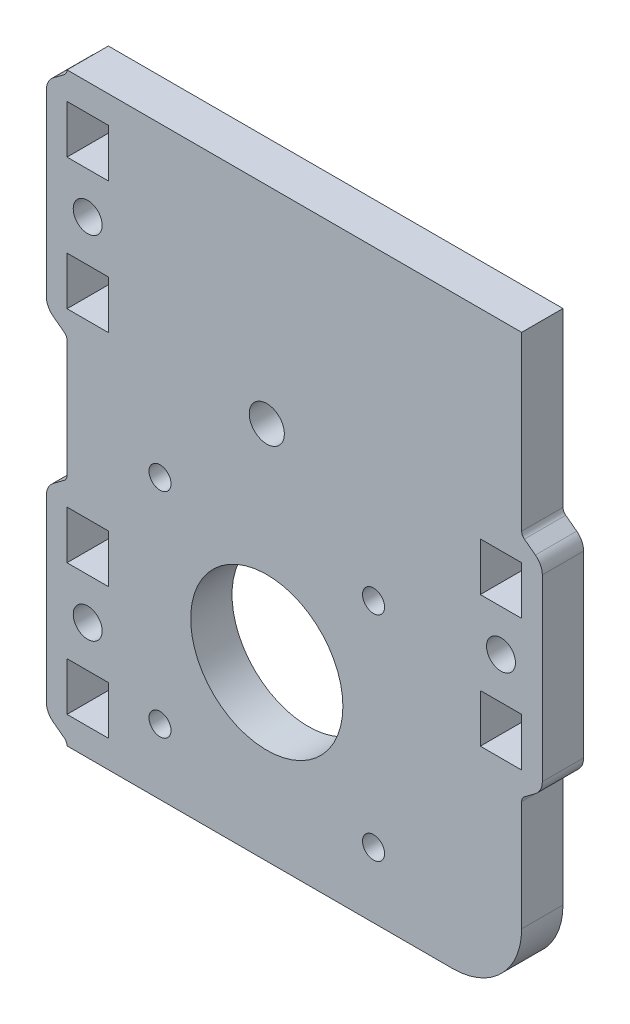
SolidWorks part; units mm, degrees
material "Клен"
ref_plane "Спереди" through (0, 0, 0) normal (0, 0, 1) x (1, 0, 0)
ref_plane "Сверху" through (0, 0, 0) normal (0, 1, 0) x (1, 0, 0)
ref_plane "Справа" through (0, 0, 0) normal (1, 0, 0) x (0, 0, -1)
sketch "Эскиз1" plane through (0, 0, 0) normal (0, 0, 1) x (1, 0, 0)
  line L7 (0, -293.8462) -> (66, -293.8462)
  line L9 (0, -378.8462) -> (0, -293.8462)
  line L11 (66, -293.8462) -> (66, -287.8462) construction
  line L12 (66, -293.8462) -> (66, -368.8462)
  line L14 (56, -378.8462) -> (0, -378.8462)
  arc A0 (66, -368.8462) -> (56, -378.8462) centre (56, -368.8462) cw
  circle A1 centre (29, -323.8462) radius 2.55
  dimension "D3" = 5.1
  dimension "D2" = 10
  dimension "D1" = 85
extrude "Бобышка-Вытянуть1" add sketch "Эскиз1" against normal blind 6 contours L14 L9 L7 L12 A0
sketch "Эскиз2" plane through (0, 0, 0) normal (0, 0, 1) x (1, 0, 0)
  line L1 (0, -378.8462) -> (0, -293.8462) construction
  line L3 (29, -353.8462) -> (54.8419, -353.8462) construction
  line L5 (0, -293.8462) -> (66, -293.8462) construction
  circle A0 centre (29, -353.8462) radius 11.05
  circle A1 centre (44.5, -369.3462) radius 1.6
  circle A2 centre (13.5, -369.3462) radius 1.6
  circle A3 centre (13.5, -338.3462) radius 1.6
  circle A4 centre (44.5, -338.3462) radius 1.6
  circle A5 centre (29, -323.8462) radius 2.55
  dimension "D2" = 22.1
  dimension "D3" = 3.2
  dimension "D6" = 5.1
  dimension "D1" = 60
  dimension "D4" = 15.5
  dimension "D5" = 15.5
  dimension "D7" = 29
extrude "Вырез-Вытянуть1" cut sketch "Эскиз2" against normal through all
sketch "Эскиз21" plane through (16, -335.8462, 0) normal (0, 0, -1) x (0, 1, 0)
  line L0 (-13, 53) -> (13, 53)
  line L2 (15, 52) -> (16.2, 50.4)
  line L4 (17, 50) -> (-17, 50)
  line L5 (-15, 52) -> (-16.2, 50.4)
  arc A6 (13, 53) -> (15, 52) centre (13, 50.5) cw
  arc A7 (16.2, 50.4) -> (17, 50) centre (17, 51) ccw
  arc A8 (-13, 53) -> (-15, 52) centre (-13, 50.5) ccw
  arc A9 (-16.2, 50.4) -> (-17, 50) centre (-17, 51) cw
  point P12 (0, 53)
  point P13 (14.118, 52.7361)
  point P15 (-14.118, 52.7361)
  point P17 (0, 50)
  point P21 (14.118, 52.7361)
  dimension "D4" = 2.5
  dimension "D5" = 1
extrude "Бобышка-Вытянуть2" add sketch "Эскиз21" along normal blind 6
sketch "Эскиз3" plane through (16, -335.8462, -6) normal (0, 0, -1) x (0, 1, 0)
  line L1 (13.0318, 50) -> (6.0318, 50)
  line L2 (13.0318, 50) -> (13.0318, 44)
  line L3 (13.0318, 44) -> (6.0318, 44)
  line L4 (6.0318, 50) -> (6.0318, 44)
  line L5 (-13.0318, 44) -> (-6.0318, 44)
  line L6 (-13.0318, 50) -> (-13.0318, 44)
  line L7 (-6.0318, 50) -> (-6.0318, 44)
  line L8 (-13.0318, 50) -> (-6.0318, 50)
  circle A0 centre (0, 47) radius 2.1
  dimension "D1" = 4.2
extrude "Вырез-Вытянуть11" cut sketch "Эскиз3" against normal through all
other "Авто-элемент1<DIN967-21>"
sketch "Эскиз22" plane through (50, -310.8462, 0) normal (0, 0, -1) x (0, -1, 0)
  line L0 (-13, 53) -> (13, 53)
  line L2 (15, 52) -> (16.2, 50.4)
  line L4 (17, 50) -> (-17, 50)
  line L5 (-15, 52) -> (-16.2, 50.4)
  arc A6 (13, 53) -> (15, 52) centre (13, 50.5) cw
  arc A7 (16.2, 50.4) -> (17, 50) centre (17, 51) ccw
  arc A8 (-13, 53) -> (-15, 52) centre (-13, 50.5) ccw
  arc A9 (-16.2, 50.4) -> (-17, 50) centre (-17, 51) cw
  point P12 (0, 53)
  point P13 (14.118, 52.7361)
  point P15 (-14.118, 52.7361)
  point P17 (0, 50)
  point P21 (14.118, 52.7361)
  dimension "D4" = 2.5
  dimension "D5" = 1
extrude "Бобышка-Вытянуть21" add sketch "Эскиз22" along normal blind 6
sketch "Эскиз31" plane through (50, -310.8462, -6) normal (0, 0, -1) x (0, -1, 0)
  line L1 (13.0318, 50) -> (6.0318, 50)
  line L2 (13.0318, 50) -> (13.0318, 44)
  line L3 (13.0318, 44) -> (6.0318, 44)
  line L4 (6.0318, 50) -> (6.0318, 44)
  line L5 (-13.0318, 44) -> (-6.0318, 44)
  line L6 (-13.0318, 50) -> (-13.0318, 44)
  line L7 (-6.0318, 50) -> (-6.0318, 44)
  line L8 (-13.0318, 50) -> (-6.0318, 50)
  circle A0 centre (0, 47) radius 2.1
  dimension "D1" = 4.2
extrude "Вырез-Вытянуть12" cut sketch "Эскиз31" against normal through all
other "Авто-элемент2<DIN967-22>"
sketch "Эскиз24" plane through (50, -361.8462, 0) normal (0, 0, -1) x (0, -1, 0)
  line L0 (-13, 53) -> (13, 53)
  line L2 (15, 52) -> (16.2, 50.4)
  line L4 (17, 50) -> (-17, 50)
  line L5 (-15, 52) -> (-16.2, 50.4)
  arc A6 (13, 53) -> (15, 52) centre (13, 50.5) cw
  arc A7 (16.2, 50.4) -> (17, 50) centre (17, 51) ccw
  arc A8 (-13, 53) -> (-15, 52) centre (-13, 50.5) ccw
  arc A9 (-16.2, 50.4) -> (-17, 50) centre (-17, 51) cw
  point P12 (0, 53)
  point P13 (14.118, 52.7361)
  point P15 (-14.118, 52.7361)
  point P17 (0, 50)
  point P21 (14.118, 52.7361)
  dimension "D4" = 2.5
  dimension "D5" = 1
extrude "Бобышка-Вытянуть24" add sketch "Эскиз24" along normal blind 6
sketch "Эскиз34" plane through (50, -361.8462, -6) normal (0, 0, -1) x (0, -1, 0)
  line L1 (13.0318, 50) -> (6.0318, 50)
  line L2 (13.0318, 50) -> (13.0318, 44)
  line L3 (13.0318, 44) -> (6.0318, 44)
  line L4 (6.0318, 50) -> (6.0318, 44)
  line L5 (-13.0318, 44) -> (-6.0318, 44)
  line L6 (-13.0318, 50) -> (-13.0318, 44)
  line L7 (-6.0318, 50) -> (-6.0318, 44)
  line L8 (-13.0318, 50) -> (-6.0318, 50)
  circle A0 centre (0, 47) radius 2.1
  dimension "D1" = 4.2
extrude "Вырез-Вытянуть15" cut sketch "Эскиз34" against normal through all
other "Авто-элемент2<DIN967_2-2>"
